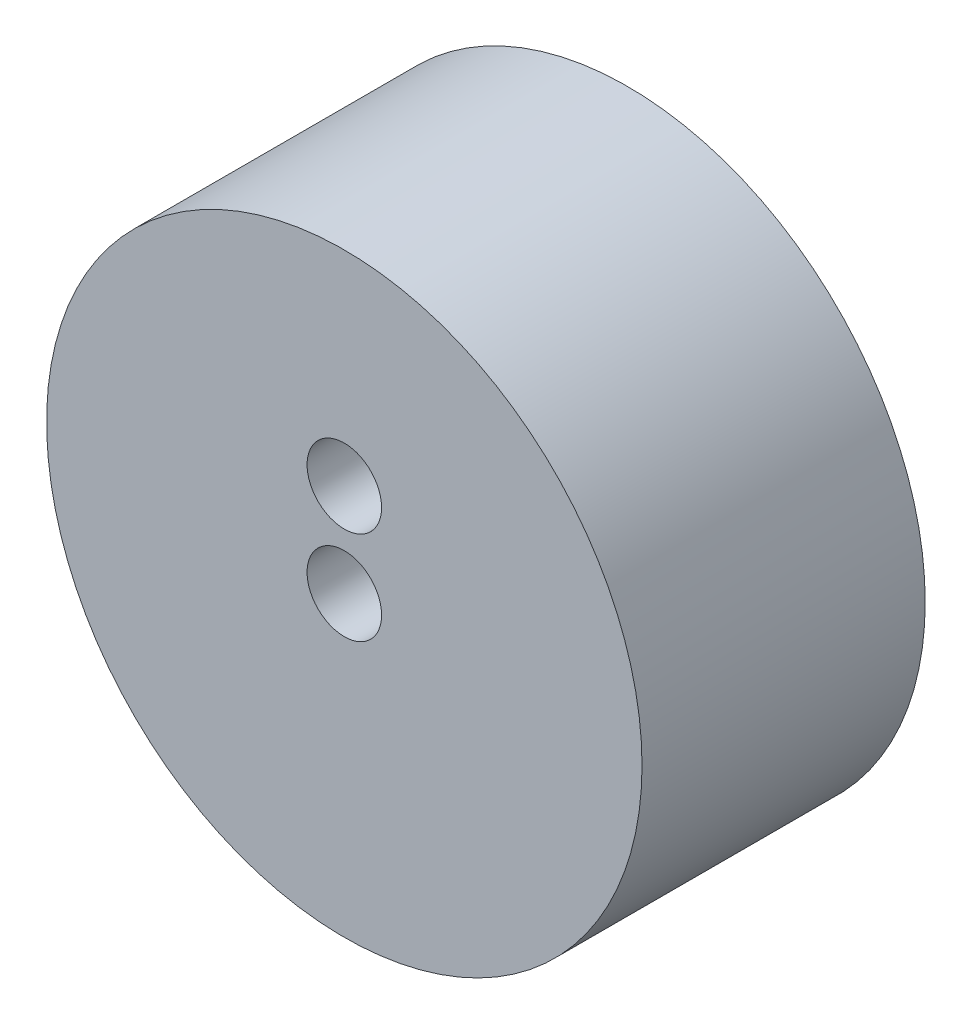
SolidWorks part; units mm, degrees
ref_plane "Front Plane" through (0, 0, 0) normal (0, 0, 1) x (1, 0, 0)
ref_plane "Top Plane" through (0, 0, 0) normal (0, 1, 0) x (1, 0, 0)
ref_plane "Right Plane" through (0, 0, 0) normal (1, 0, 0) x (0, 0, -1)
sketch "Sketch1" plane through (0, 0, 0) normal (0, 0, 1) x (1, 0, 0)
  circle A0 centre (0, 0) radius 15.98
extrude "Extrude1" add sketch "Sketch1" along normal blind 15.2
sketch "Sketch8" plane through (0, 0, 15.2) normal (0, 0, 1) x (1, 0, 0)
  circle A0 centre (0, 0) radius 2
extrude "Extrude3" cut sketch "Sketch8" against normal through all
sketch "Sketch9" plane through (0, 0, 15.2) normal (0, 0, 1) x (1, 0, 0)
  circle A0 centre (0, 5) radius 2
extrude "Extrude4" cut sketch "Sketch9" against normal through all
